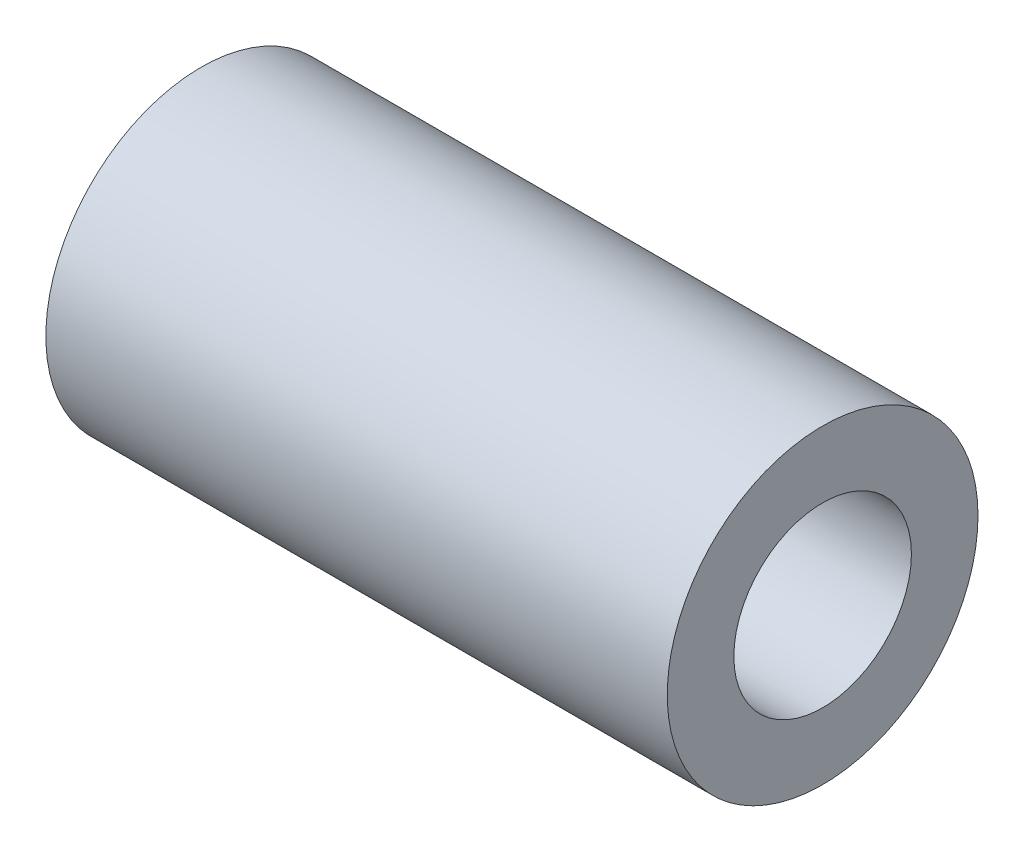
SolidWorks part; units mm, degrees
ref_plane "Alzado" through (0, 0, 0) normal (0, 0, 1) x (1, 0, 0)
ref_plane "Planta" through (0, 0, 0) normal (0, 1, 0) x (1, 0, 0)
ref_plane "Vista lateral" through (0, 0, 0) normal (1, 0, 0) x (0, 0, -1)
sketch "Croquis1" plane through (0, 0, 0) normal (1, 0, 0) x (0, 0, -1)
  circle A0 centre (0, 0) radius 4
  circle A1 centre (0, 0) radius 7
  dimension "D1" = 8
  dimension "D2" = 14
extrude "Saliente-Extruir1" add sketch "Croquis1" against normal blind 28
